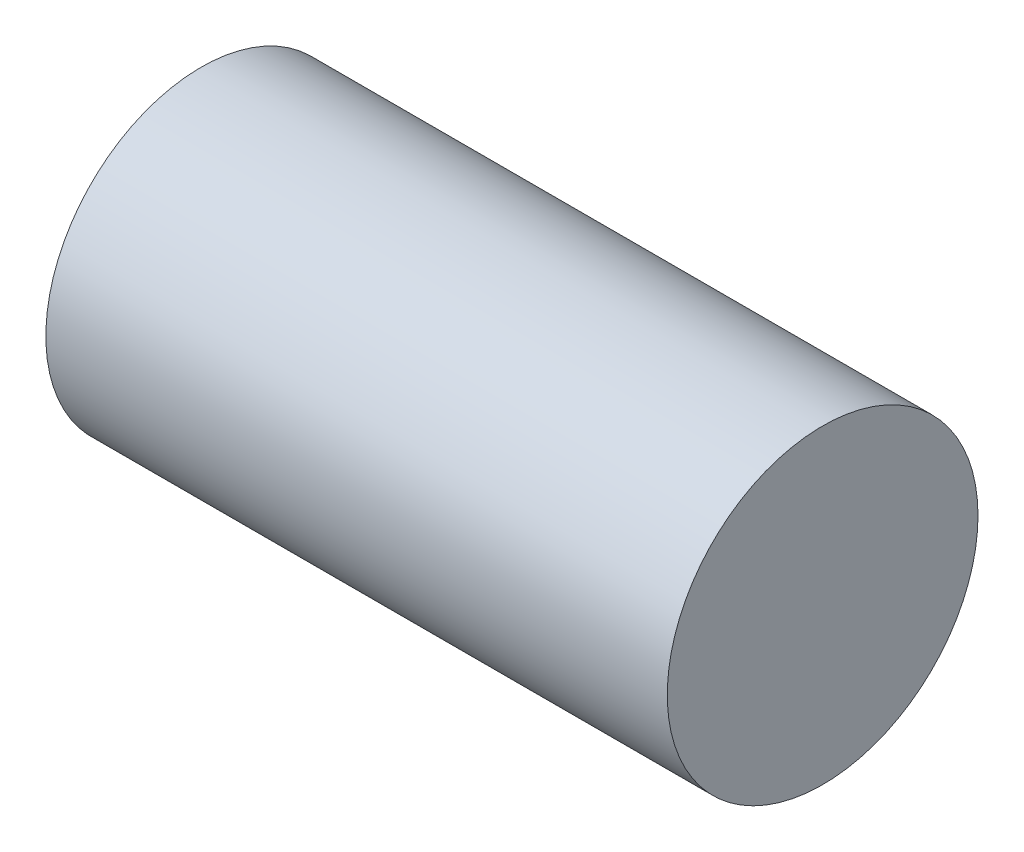
SolidWorks part; units mm, degrees
material "Brass"
ref_plane "Front Plane" through (0, 0, 0) normal (0, 0, 1) x (1, 0, 0)
ref_plane "Top Plane" through (0, 0, 0) normal (0, 1, 0) x (1, 0, 0)
ref_plane "Right Plane" through (0, 0, 0) normal (1, 0, 0) x (0, 0, -1)
sketch "Sketch1" plane through (0, 0, 0) normal (1, 0, 0) x (0, 0, -1)
  circle A0 centre (0, 0) radius 15
  dimension "D1" = 30
extrude "Boss-Extrude1" add sketch "Sketch1" along normal blind 60
